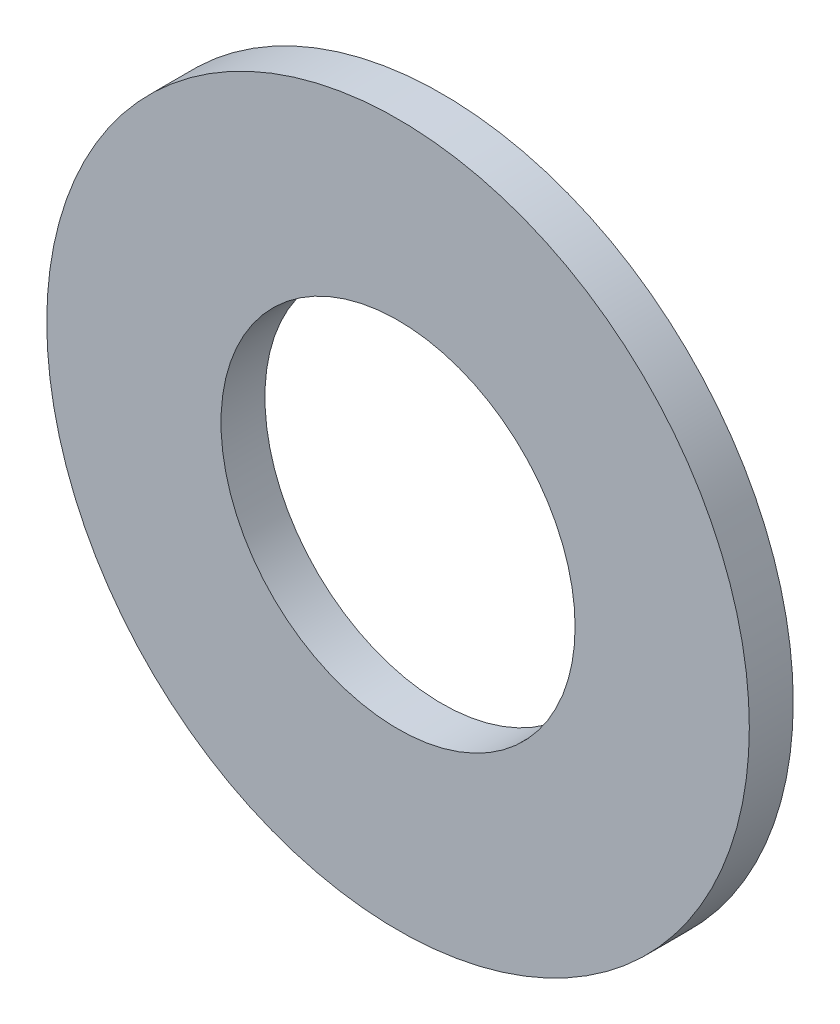
SolidWorks part; units mm, degrees
ref_plane "Front Plane" through (0, 0, 0) normal (0, 0, 1) x (1, 0, 0)
ref_plane "Top Plane" through (0, 0, 0) normal (0, 1, 0) x (1, 0, 0)
ref_plane "Right Plane" through (0, 0, 0) normal (1, 0, 0) x (0, 0, -1)
sketch "Sketch1" plane through (0, 0, 0) normal (0, 0, 1) x (1, 0, 0)
  circle A0 centre (0, 0) radius 12.7
  circle A1 centre (0, 0) radius 6.4008
  dimension "D1" = 25.4
  dimension "ID" = 12.8016
extrude "Extrude1" add sketch "Sketch1" along normal mid plane 1.5875
sketch "Sketch2" plane through (0, 0, 0) normal (1, 0, 0) x (0, 0, -1)
  line L0 (-0.7937, -6.4008) -> (0.7937, -6.4008) construction
  line L3 (0.7937, 6.4008) -> (-0.7937, 6.4008) construction
  line L5 (-0.7937, -6.4008) -> (0.7937, -6.4008)
  line L6 (0.7937, 6.4008) -> (-0.7937, 6.4008)
sketch "Sketch4" plane through (0, 0, 0.7937) normal (0, 0, 1) x (1, 0, 0)
  line L0 (0, 0) -> (-4.526, 4.526)
  line L1 (0, -0.8731) -> (0, 0.8731) construction
  circle A0 centre (0, 0) radius 6.4008 construction
  dimension "D1" = 45
